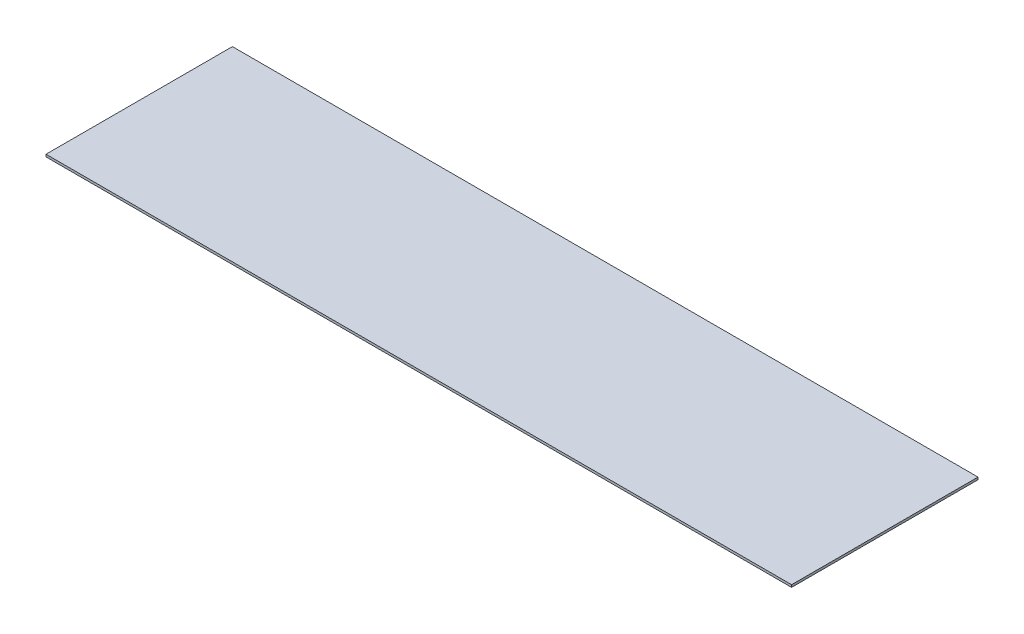
SolidWorks part; units mm, degrees
ref_plane "Front Plane" through (0, 0, 0) normal (0, 0, 1) x (1, 0, 0)
ref_plane "Top Plane" through (0, 0, 0) normal (0, 1, 0) x (1, 0, 0)
ref_plane "Right Plane" through (0, 0, 0) normal (1, 0, 0) x (0, 0, -1)
sketch "Sketch1" plane through (0, 0, 0) normal (0, 1, 0) x (1, 0, 0)
  line L1 (0, 0) -> (508, 0)
  line L2 (0, 0) -> (0, 127)
  line L3 (0, 127) -> (508, 127)
  line L4 (508, 0) -> (508, 127)
  dimension "D1" = 508
  dimension "D2" = 127
extrude "Boss-Extrude1" add sketch "Sketch1" along normal blind 1.6
